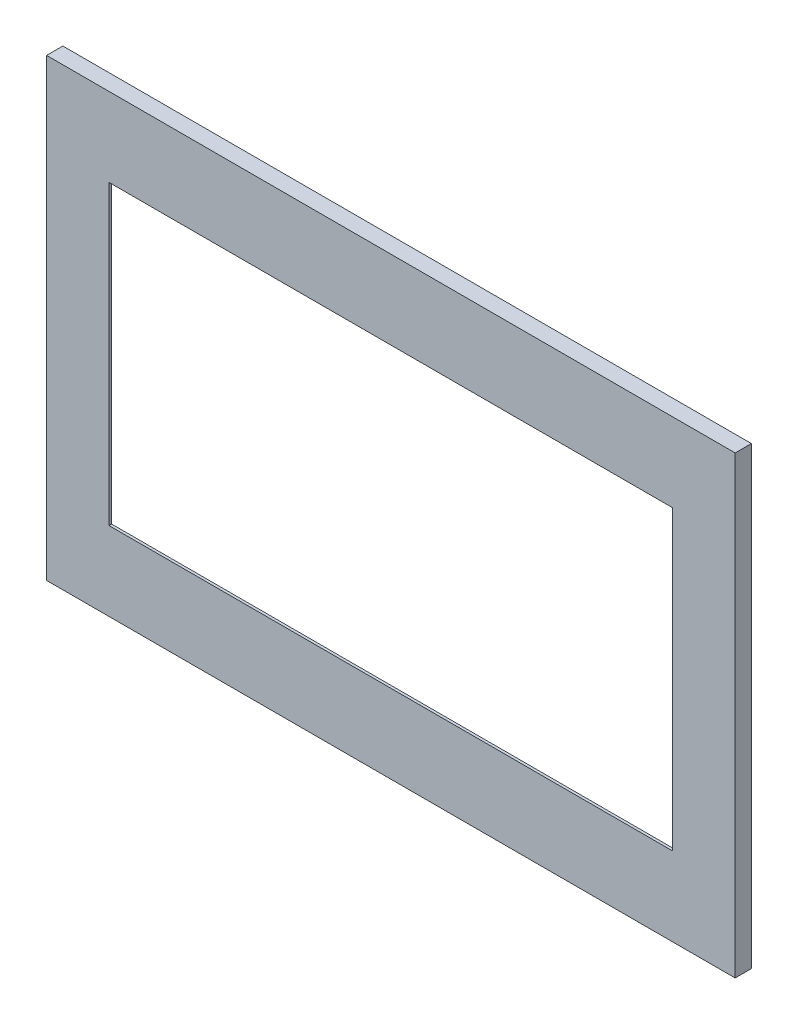
SolidWorks part; units mm, degrees
ref_plane "Front Plane" through (0, 0, 0) normal (0, 0, 1) x (1, 0, 0)
ref_plane "Top Plane" through (0, 0, 0) normal (0, 1, 0) x (1, 0, 0)
ref_plane "Right Plane" through (0, 0, 0) normal (1, 0, 0) x (0, 0, -1)
sketch "Sketch1" plane through (0, 0, 0) normal (0, 0, 1) x (1, 0, 0)
  line L1 (336.55, 222.25) -> (-336.55, 222.25)
  line L2 (336.55, 222.25) -> (336.55, -222.25)
  line L3 (336.55, -222.25) -> (-336.55, -222.25)
  line L4 (-336.55, 222.25) -> (-336.55, -222.25)
  line L5 (336.55, 222.25) -> (-336.55, -222.25) construction
  line L6 (336.55, -222.25) -> (-336.55, 222.25) construction
  point P0 (0, 0)
  dimension "D1" = 444.5
  dimension "D2" = 673.1
extrude "Boss-Extrude1" add sketch "Sketch1" along normal mid plane 15.875
sketch "Sketch2" plane through (0, 0, 7.9375) normal (0, 0, 1) x (1, 0, 0)
  line L0 (0, 0) -> (0, -222.25) construction
  line L1 (300.8312, 170.6562) -> (-300.8313, 170.6562)
  line L2 (300.8312, 170.6562) -> (300.8312, -170.6562)
  line L3 (300.8312, -170.6562) -> (-300.8313, -170.6562)
  line L4 (-300.8313, 170.6562) -> (-300.8313, -170.6562)
  line L5 (300.8312, 170.6562) -> (-300.8313, -170.6562) construction
  line L6 (300.8312, -170.6562) -> (-300.8313, 170.6562) construction
  line L7 (-336.55, -222.25) -> (336.55, -222.25) construction
  point P0 (0, 0)
  dimension "D1" = 341.3125
  dimension "D2" = 601.6625
extrude "Cut-Extrude1" cut sketch "Sketch2" against normal through all both and the other way through all
sketch "Sketch4" plane through (0, 0, 7.9375) normal (0, 0, 1) x (1, 0, 0)
  line L0 (-336.55, 222.25) -> (-336.55, -222.25) construction
  line L1 (-336.55, 203.2) -> (-344.4875, 203.2)
  line L2 (-336.55, 203.2) -> (-336.55, -203.2)
  line L3 (-336.55, -203.2) -> (-344.4875, -203.2)
  line L4 (-344.4875, 203.2) -> (-344.4875, -203.2)
  line L5 (336.55, -222.25) -> (336.55, 222.25) construction
  line L6 (336.55, 203.2) -> (344.4875, 203.2)
  line L7 (336.55, 203.2) -> (336.55, -203.2)
  line L8 (336.55, -203.2) -> (344.4875, -203.2)
  line L9 (344.4875, 203.2) -> (344.4875, -203.2)
  line L10 (336.55, 222.25) -> (-336.55, 222.25) construction
  line L15 (0, 0) -> (0, 230.1875) construction
  line L16 (-336.55, -222.25) -> (336.55, -222.25) construction
  dimension "D1" = 19.05
  dimension "D2" = 19.05
  dimension "D3" = 7.9375
  dimension "D4" = 688.975
extrude "Boss-Extrude2" [suppressed] add sketch "Sketch4" against normal up to surface (15.875 mm away)
fillet "Fillet1" [suppressed] radius 6.35
sketch "Sketch6" plane through (336.55, 0, 0) normal (1, 0, 0) x (0, 0, -1)
  line L0 (-7.9375, -222.25) -> (7.9375, -215.6744)
  line L2 (7.9375, -215.6744) -> (7.9375, -222.25)
  line L3 (7.9375, -222.25) -> (-7.9375, -222.25)
  dimension "D1" = 22.5
extrude "Cut-Extrude4" [suppressed] cut sketch "Sketch6" against normal through all both and the other way through all
sketch "Sketch7" plane through (0, 0, -7.9375) normal (0, 0, -1) x (-1, 0, 0)
  line L0 (0, 187.325) -> (0, -187.325) construction
  line L1 (-314.325, 0) -> (314.325, 0) construction
  line L2 (300.8313, -170.6562) -> (-300.8312, -170.6562) construction
  line L3 (-300.8312, 170.6562) -> (300.8313, 170.6562) construction
  line L15 (-307.975, -187.325) -> (307.975, -187.325)
  line L16 (314.325, -180.975) -> (314.325, 180.975)
  line L17 (307.975, 187.325) -> (-307.975, 187.325)
  line L18 (-314.325, 180.975) -> (-314.325, -180.975)
  arc A0 (314.325, 180.975) -> (307.975, 187.325) centre (307.975, 180.975) ccw
  arc A1 (307.975, -187.325) -> (314.325, -180.975) centre (307.975, -180.975) ccw
  arc A2 (-307.975, -187.325) -> (-314.325, -180.975) centre (-307.975, -180.975) cw
  arc A3 (-307.975, 187.325) -> (-314.325, 180.975) centre (-307.975, 180.975) ccw
  dimension "D2" = 6.35
  dimension "D1" = 628.65
  dimension "D3" = 374.65
  dimension "D4" = 16.6688
  dimension "D5" = 16.6687
extrude "Cut-Extrude5" [suppressed] cut sketch "Sketch7" against normal blind 9.525
sketch "Sketch8" plane through (0, 0, 7.9375) normal (0, 0, 1) x (1, 0, 0)
  line L0 (300.8312, -170.6562) -> (-300.8313, -170.6562) construction
  line L1 (300.8312, 170.6562) -> (-300.8313, 170.6562)
  line L2 (300.8312, 170.6562) -> (300.8312, -170.6562)
  line L3 (300.8312, -170.6562) -> (-300.8313, -170.6562)
  line L4 (-300.8313, 170.6562) -> (-300.8313, -170.6562)
  line L5 (-300.8313, 170.6562) -> (300.8312, 170.6562) construction
  line L6 (300.8312, 170.6562) -> (300.8312, -170.6562) construction
  line L8 (275.4312, 145.2562) -> (-275.4313, 145.2562)
  line L9 (275.4312, 145.2562) -> (275.4312, -145.2562)
  line L10 (275.4312, -145.2562) -> (-275.4313, -145.2562)
  line L11 (-275.4313, 145.2562) -> (-275.4313, -145.2562)
  point P0 (0, 0)
  point P8 (0, 3.81)
  point P15 (0, 170.6562)
  dimension "D1" = 25.4
  dimension "D2" = 25.4
  dimension "D3" = 25.4
  dimension "D4" = 25.4
extrude "Boss-Extrude3" add sketch "Sketch8" against normal blind 2.54
sketch "Sketch9" [suppressed] plane through (0, 0, 7.9375) normal (0, 0, 1) x (1, 0, 0)
  line L8 (-319.8813, -184.15) -> (319.8812, -184.15)
  line L9 (319.8812, -184.15) -> (319.8812, 195.2625)
  line L10 (319.8812, 195.2625) -> (-319.8813, 195.2625)
  line L11 (-319.8813, 195.2625) -> (-319.8813, -184.15)
  line L12 (-319.8813, -184.15) -> (319.8812, -184.15)
  line L13 (319.8812, -184.15) -> (319.8812, 195.2625)
  line L14 (319.8812, 195.2625) -> (-319.8813, 195.2625)
  line L15 (-319.8813, 195.2625) -> (-319.8813, -184.15)
  dimension "D1" = 19.05
sketch "Sketch10" [suppressed] plane through (0, 0, -7.9375) normal (0, 0, -1) x (-1, 0, 0)
  line L0 (-300.8312, 176.2125) -> (300.8313, 176.2125) construction
  line L1 (300.8313, 176.2125) -> (300.8313, -165.1) construction
  line L2 (-300.8312, -165.1) -> (-300.8312, 176.2125) construction
  line L3 (300.8313, -165.1) -> (-300.8312, -165.1) construction
  line L4 (-300.8312, 176.2125) -> (300.8313, 176.2125)
  line L5 (300.8313, 176.2125) -> (300.8313, -165.1)
  line L6 (-300.8312, -165.1) -> (-300.8312, 176.2125)
  line L7 (300.8313, -165.1) -> (-300.8312, -165.1)
loft "Cut-Loft1" [suppressed] cut profiles "Sketch9", "Sketch10"
